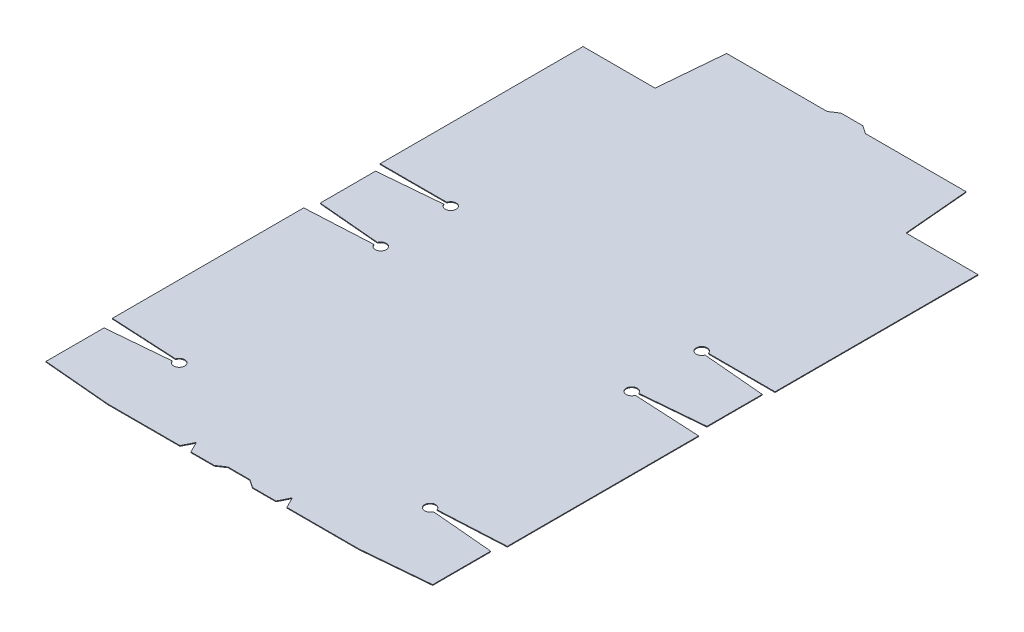
SolidWorks part; units mm, degrees
material "CHIP BOARD"
ref_plane "Front Plane" through (0, 0, 0) normal (0, 0, 1) x (1, 0, 0)
ref_plane "Top Plane" through (0, 0, 0) normal (0, 1, 0) x (1, 0, 0)
ref_plane "Right Plane" through (0, 0, 0) normal (1, 0, 0) x (0, 0, -1)
sketch "Sketch1" plane through (0, 0, 0) normal (0, 1, 0) x (1, 0, 0)
  line L0 (145.2563, 434.1812) -> (138.0341, 516.7312)
  line L1 (-146.05, 116.6813) -> (146.05, 116.6813) construction
  line L3 (145.2562, -199.2313) -> (223.8375, -192.3563)
  line L5 (-146.05, -116.6813) -> (146.05, -116.6813) construction
  line L6 (228.6, 434.1812) -> (228.6, 199.2312) construction
  line L7 (-145.2562, -199.2313) -> (145.2562, -199.2313)
  line L8 (146.05, 199.2312) -> (146.05, 116.6812) construction
  line L9 (-145.2562, -199.2313) -> (-223.8375, -192.3563)
  line L10 (228.6, -110.7237) -> (145.1732, -115.0959)
  line L11 (-228.6, -110.7237) -> (-145.1732, -115.0959)
  line L12 (-228.6, -110.7237) -> (-228.6, 110.7237)
  line L14 (223.8375, -192.3563) -> (223.8375, -125.1498)
  line L15 (223.8375, -125.1498) -> (145.1179, -118.2627)
  line L16 (-138.0341, 516.7312) -> (-145.2563, 434.1812)
  line L18 (145.2563, 434.1812) -> (228.6, 434.1812)
  line L19 (145.1179, 196.0623) -> (223.8375, 189.1752)
  line L21 (228.6, -110.7237) -> (228.6, 110.7237)
  line L22 (-145.2563, 434.1812) -> (-228.6, 434.1812)
  line L23 (228.6, 199.2312) -> (145.2562, 199.2312)
  line L24 (-228.6, 110.7237) -> (-145.1732, 115.0959)
  line L25 (223.8375, 189.1752) -> (223.8375, 125.1498)
  line L26 (228.6, 110.7237) -> (145.1732, 115.0959)
  line L27 (223.8375, 125.1498) -> (145.1179, 118.2627)
  line L28 (-228.6, 199.2312) -> (-145.2562, 199.2312)
  line L29 (0, 0) -> (0, 116.6812) construction
  line L32 (-145.1179, 196.0623) -> (-223.8375, 189.1752)
  line L33 (146.05, 116.6813) -> (146.05, -116.6813) construction
  line L34 (-146.05, 199.2312) -> (228.6, 199.2312) construction
  line L35 (145.2562, -116.6813) -> (145.2562, -199.2313) construction
  line L36 (-145.2562, -199.2313) -> (-145.2562, -116.6813) construction
  line L37 (-223.8375, 189.1752) -> (-223.8375, 125.1498)
  line L38 (-223.8375, 125.1498) -> (-145.1179, 118.2627)
  line L39 (228.6, 199.2312) -> (228.6, 434.1812)
  line L40 (-146.05, -116.6813) -> (-146.05, 116.6813) construction
  line L41 (-146.05, 116.6812) -> (-146.05, 199.2312) construction
  line L42 (-228.6, 434.1812) -> (-228.6, 199.2312) construction
  line L43 (-228.6, 434.1812) -> (228.6, 434.1812) construction
  line L44 (-138.0341, 516.7312) -> (138.0341, 516.7312)
  line L45 (0, 0) -> (-146.05, 0) construction
  line L48 (-228.6, 434.1812) -> (-228.6, 199.2312)
  line L49 (-223.8375, -192.3563) -> (-223.8375, -125.1498)
  line L50 (-223.8375, -125.1498) -> (-145.1179, -118.2627)
  arc A0 (-145.1179, -118.2627) -> (-145.1732, -115.0959) centre (-145.2562, -116.6813) ccw
  arc A1 (145.1732, -115.0959) -> (145.1179, -118.2627) centre (145.2562, -116.6813) ccw
  arc A2 (145.1179, 118.2627) -> (145.1732, 115.0959) centre (145.2562, 116.6812) ccw
  arc A3 (-145.1732, 115.0959) -> (-145.1179, 118.2627) centre (-145.2562, 116.6812) ccw
  arc A4 (-145.1179, 196.0623) -> (-145.2562, 199.2312) centre (-145.2562, 197.6437) ccw
  arc A5 (145.2562, 199.2312) -> (145.1179, 196.0623) centre (145.2562, 197.6437) ccw
  point P4 (0, 116.6812)
  dimension "D5" = 1.5875
  dimension "E1" = 82.55
  dimension "D6" = 93
  dimension "D7" = 5
  dimension "D10" = 95
  dimension "D14" = 95
  dimension "D15" = 93
  dimension "D16" = 0.7937
  dimension "D17" = 715.9625
  dimension "D18" = 93
  dimension "D19" = 95
  dimension "D21" = 95
  dimension "E2" = 82.55
  dimension "A1" = 233.3625
  dimension "A2" = 234.95
  dimension "E3" = 82.55
  dimension "C1" = 292.1
  dimension "C2" = 292.1
  dimension "E4" = 82.55
  dimension "B1" = 447.675
extrude "Extrude1" add sketch "Sketch1" along normal blind 0.7937
sketch "Sketch2" plane through (0, 0.7937, 0) normal (0, 1, 0) x (1, 0, 0)
  circle A0 centre (-145.2562, 116.6812) radius 6.35
  circle A1 centre (-145.2562, -116.6813) radius 6.35
  circle A2 centre (145.2562, -116.6813) radius 6.35
  circle A3 centre (145.2562, 116.6812) radius 6.35
  circle A4 centre (-145.2562, 197.6437) radius 6.35
  circle A5 centre (145.2562, 197.6437) radius 6.35
  arc A6 (145.1732, -115.0959) -> (145.1179, -118.2627) centre (145.2562, -116.6813) ccw construction
  arc A7 (-145.1179, 196.0623) -> (-145.2562, 199.2312) centre (-145.2562, 197.6437) ccw construction
  arc A8 (-145.1732, 115.0959) -> (-145.1179, 118.2627) centre (-145.2562, 116.6812) ccw construction
  arc A9 (-145.1179, -118.2627) -> (-145.1732, -115.0959) centre (-145.2562, -116.6813) ccw construction
  arc A10 (145.1179, 118.2627) -> (145.1732, 115.0959) centre (145.2562, 116.6812) ccw construction
  arc A11 (145.2562, 199.2312) -> (145.1179, 196.0623) centre (145.2562, 197.6437) ccw construction
  dimension "D1" = 12.7
extrude "Extrude2" cut sketch "Sketch2" against normal up to next
sketch "Sketch12" plane through (0, 0.7937, 0) normal (0, 1, 0) x (1, 0, 0)
  line L0 (-138.5896, 510.3813) -> (-22.225, 510.3813)
  line L1 (-138.0341, 516.7312) -> (-145.2563, 434.1812) construction
  line L2 (-22.225, 510.3813) -> (-12.7, 516.7312)
  line L3 (138.0341, 516.7312) -> (-138.0341, 516.7312) construction
  line L4 (12.7, 516.7312) -> (22.225, 510.3813)
  line L5 (22.225, 510.3813) -> (138.5896, 510.3813)
  line L6 (145.2563, 434.1812) -> (138.0341, 516.7312) construction
  line L7 (138.5896, 510.3813) -> (138.0341, 516.7312)
  line L8 (138.0341, 516.7312) -> (12.7, 516.7312)
  line L9 (-12.7, 516.7312) -> (-138.0341, 516.7312)
  line L10 (-138.0341, 516.7312) -> (-138.5896, 510.3813)
  dimension "D1" = 6.35
  dimension "D2" = 25.4
  dimension "D3" = 44.45
extrude "Extrude3" cut sketch "Sketch12" against normal up to next
sketch "Sketch13" plane through (0, 0.7937, 0) normal (0, 1, 0) x (1, 0, 0)
  line L0 (-61.9125, -199.2313) -> (-55.5625, -186.5313)
  line L1 (-145.2562, -199.2313) -> (145.2562, -199.2313) construction
  line L2 (-55.5625, -186.5313) -> (-49.2125, -199.2313)
  line L3 (-49.2125, -199.2313) -> (-61.9125, -199.2313)
  line L4 (49.2125, -199.2313) -> (55.5625, -186.5313)
  line L5 (55.5625, -186.5313) -> (61.9125, -199.2313)
  line L6 (49.2125, -199.2313) -> (61.9125, -199.2313)
  line L7 (-55.5625, -186.5313) -> (55.5625, -186.5313) construction
  line L8 (-55.5625, -186.5313) -> (-55.5625, -199.2313) construction
  line L9 (55.5625, -186.5313) -> (55.5625, -199.2313) construction
  line L10 (-22.225, -199.2313) -> (-12.7, -192.8813)
  line L11 (-12.7, -192.8813) -> (12.7, -192.8813)
  line L12 (12.7, -192.8813) -> (22.225, -199.2313)
  line L13 (22.225, -199.2313) -> (-22.225, -199.2313)
  point P7 (0, -186.5313)
  point P14 (0, -192.8813)
  point P17 (0, -199.2313)
  dimension "D1" = 12.7
  dimension "D2" = 111.125
  dimension "D3" = 12.7
  dimension "D4" = 6.35
  dimension "D5" = 25.4
  dimension "D6" = 44.45
extrude "Extrude4" cut sketch "Sketch13" against normal up to next
sheet metal parameters "Sheet-Metal1" parameters "D1"=0.7937
flatten bends "Flatten-Bends1" [suppressed] parameters "D1"=0
sketch "Sharp-Sketch1" [suppressed] plane through (0, 0.7937, 0) normal (0, 1, 0) x (-1, 0, 0)
process bends "Process-Bends1" [suppressed] parameters "D1"=0
sketch "Flat-Sketch1" [suppressed] plane through (0, 0.7937, 0) normal (0, 1, 0) x (-1, 0, 0)
sketch "Sketch3" [suppressed] plane through (0, 0.7937, 0) normal (0, 1, 0) x (1, 0, 0)
  line L0 (-146.05, -122.9814) -> (-146.05, -199.2313)
  line L2 (-145.2562, -199.2313) -> (145.2562, -199.2313) construction
  line L5 (-146.05, -199.2313) -> (146.05, -199.2313) construction
  line L6 (146.05, -122.9814) -> (146.05, -199.2313)
  arc A0 (151.3131, -114.7741) -> (151.2429, -118.7986) centre (145.2562, -116.6813) ccw construction
  arc A1 (-151.2429, -118.7986) -> (-151.3131, -114.7741) centre (-145.2562, -116.6813) ccw construction
  point P2 (0, -199.2313)
  dimension "D1" = 292.1
sketched bend "Sketched Bend10" [suppressed] parameters "D1"=0.7937
bend "SketchBend19" [suppressed] bend radius 0.7937 bend angle 90 parameters "D5"=7
bend "SketchBend20" [suppressed] bend radius 0 bend angle 90 parameters "D5"=8
sketch "Sketch7" [suppressed] plane through (0, 0.7937, 0) normal (0, 1, 0) x (1, 0, 0)
  line L0 (-146.8438, 110.5329) -> (-146.8438, -110.5329)
  line L1 (146.8438, 110.5329) -> (146.8438, -110.5329)
  line L2 (-146.8438, -110.5329) -> (146.8438, -110.5329) construction
  arc A0 (-151.3131, 114.7741) -> (-151.2429, 118.7986) centre (-145.2562, 116.6812) ccw construction
  arc A1 (151.3131, -114.7741) -> (151.2429, -118.7986) centre (145.2562, -116.6813) ccw construction
  arc A2 (-151.2429, -118.7986) -> (-151.3131, -114.7741) centre (-145.2562, -116.6813) ccw construction
  arc A4 (151.2429, 118.7986) -> (151.3131, 114.7741) centre (145.2562, 116.6812) ccw construction
  point P5 (0, -110.5329)
  dimension "D1" = 293.6875
sketch "Sketch11" [suppressed] plane through (0, 0.7937, 0) normal (0, 1, 0) x (1, 0, 0)
  line L0 (-146.05, 191.3436) -> (-146.05, 122.9814)
  line L1 (146.05, 191.3436) -> (146.05, 122.9814)
  line L2 (-146.05, 122.9814) -> (146.05, 122.9814) construction
  arc A0 (-151.2429, 195.5264) -> (-151.4046, 199.2312) centre (-145.2562, 197.6437) ccw construction
  arc A2 (151.4046, 199.2312) -> (151.2429, 195.5264) centre (145.2562, 197.6437) ccw construction
  arc A4 (151.2429, 118.7986) -> (151.3131, 114.7741) centre (145.2562, 116.6812) ccw construction
  arc A5 (-151.3131, 114.7741) -> (-151.2429, 118.7986) centre (-145.2562, 116.6812) ccw construction
  point P16 (0, 122.9814)
  dimension "D1" = 292.1
sketched bend "Sketched Bend9" [suppressed] parameters "D1"=0
bend "SketchBend17" [suppressed] bend radius 0.7937 bend angle 90 parameters "D5"=5
bend "SketchBend18" [suppressed] bend radius 0 bend angle 90 parameters "D5"=6
sketch "Sketch8" [suppressed] plane through (0, 0.7937, 0) normal (0, 1, 0) x (1, 0, 0)
  line L0 (-151.6062, 116.6813) -> (151.6062, 116.6813)
  line L1 (138.9063, -116.6813) -> (-138.9062, -116.6813)
  line L3 (0, 116.6812) -> (0, -116.6812) construction
  arc A2 (-151.2429, -118.7986) -> (-151.3131, -114.7741) centre (-145.2562, -116.6813) ccw construction
  circle A3 centre (145.2562, -116.6813) radius 6.35 construction
  arc A5 (-151.3131, 114.7741) -> (-151.2429, 118.7986) centre (-145.2562, 116.6812) ccw construction
  arc A7 (151.2429, 118.7986) -> (151.3131, 114.7741) centre (145.2562, 116.6812) ccw construction
  point P28 (0, 0)
  dimension "D1" = 233.3625
sketched bend "Sketched Bend5" [suppressed] parameters "D1"=1.5875
bend "SketchBend9" [suppressed] bend radius 1.5875 bend angle 90 parameters "D5"=3
bend "SketchBend10" [suppressed] bend radius 1.5875 bend angle 90 parameters "D5"=4
sketched bend "Sketched Bend6" [suppressed] parameters "D1"=1.5875
bend "SketchBend11" [suppressed] bend radius 1.5875 bend angle 90 parameters "D5"=1
bend "SketchBend12" [suppressed] bend radius 1.5875 bend angle 90 parameters "D5"=2
flat pattern "Flat-Pattern1" [suppressed]
sketch "Bend-Lines1" [suppressed] plane through (0, 0.4572, 0) normal (0, 1, 0) x (-1, 0, 0)
sketch3d "Bounding-Box1" [suppressed]
  line L0 (383.3812, -274.6375, 0) -> (383.3812, 360.3625, 0) construction
  line L1 (-89.6938, -274.6375, 0) -> (-89.6938, 360.3625, 0) construction
  line L2 (383.3812, -274.6375, 0) -> (-89.6938, -274.6375, 0) construction
  line L3 (383.3812, 360.3625, 0) -> (-89.6938, 360.3625, 0) construction
bend of the flat pattern "Flatten-<SketchBend11>1"
bend of the flat pattern "Flatten-<SketchBend12>1"
bend of the flat pattern "Flatten-<SketchBend9>1"
bend of the flat pattern "Flatten-<SketchBend10>1"
bend of the flat pattern "Flatten-<SketchBend17>1"
bend of the flat pattern "Flatten-<SketchBend18>1"
bend of the flat pattern "Flatten-<SketchBend19>1"
bend of the flat pattern "Flatten-<SketchBend20>1"
